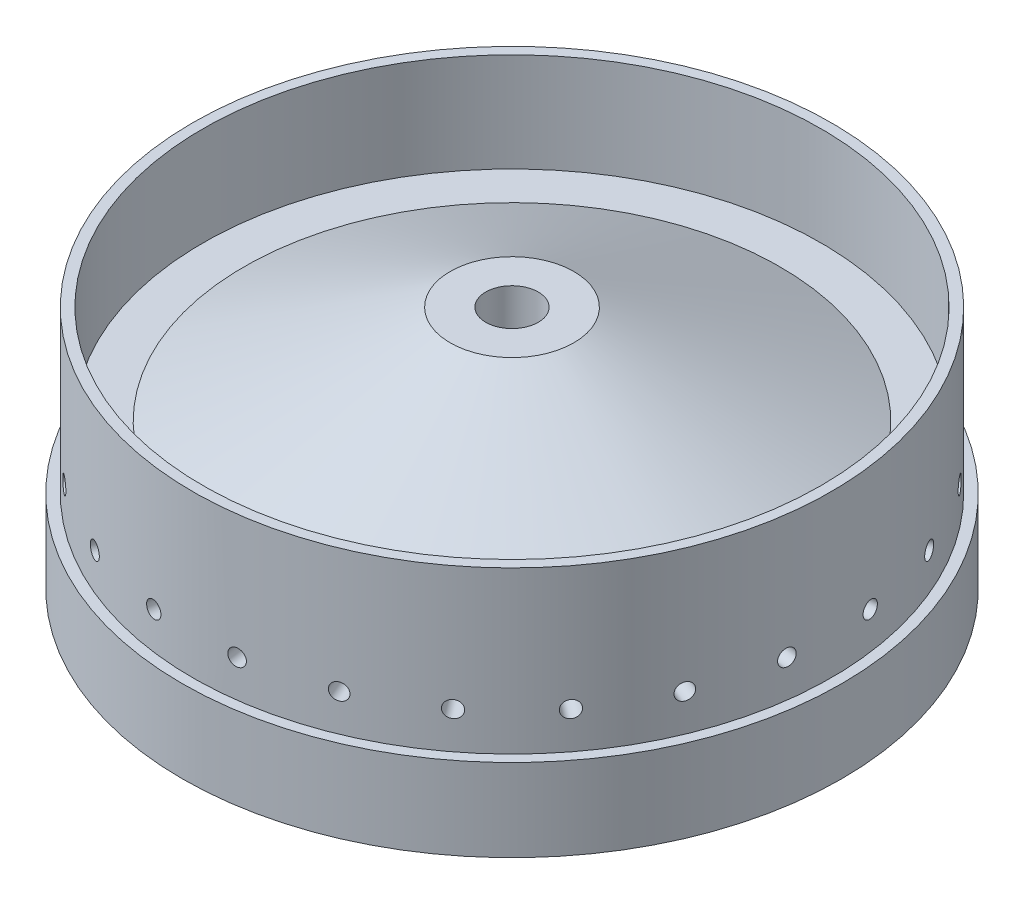
SolidWorks part; units mm, degrees
material "6061-T4 (SS)"
ref_plane "Front Plane" through (0, 0, 0) normal (0, 0, 1) x (1, 0, 0)
ref_plane "Top Plane" through (0, 0, 0) normal (0, 1, 0) x (1, 0, 0)
ref_plane "Right Plane" through (0, 0, 0) normal (1, 0, 0) x (0, 0, -1)
ref_plane "Plane1" through (0, 0, -75.0887) normal (0, 0, 1) x (1, 0, 0)
sketch "Sketch1" plane through (0, 0, 0) normal (0, 1, 0) x (1, 0, 0)
  line L1 (95.25, 0) -> (101.6, 0)
  line L2 (0, 0) -> (0, 61.9125) construction
  line L4 (101.6, 59.4931) -> (101.6, 0)
  line L6 (101.6, 59.4931) -> (8.0962, 59.4931) construction
  line L8 (0, 75.0887) -> (101.6, 75.0887)
  line L9 (101.6, 75.0887) -> (101.6, 59.4931)
  line L10 (8.0962, 0) -> (8.0962, 75.0887)
  line L11 (8.0962, 75.0887) -> (-8.0962, 75.0887)
  line L12 (-8.0962, 75.0887) -> (-8.0962, 0)
  line L13 (-8.0962, 0) -> (8.0962, 0)
  line L14 (8.0962, 59.4931) -> (0, 59.4931) construction
  line L15 (19.05, 75.0887) -> (82.55, 44.6088)
  line L16 (82.55, 44.6088) -> (95.25, 44.6088)
  line L17 (95.25, 44.6088) -> (95.25, 75.0887)
  ellipse E0 centre (0, 0) end of major axis (-95.25, 0) minor radius 59.4931
  point P18 (19.05, 75.0887)
  dimension "D4" = 15.5956
  dimension "D6" = 16.1925
  dimension "D7" = 6.35
  dimension "D8" = 30.48
  dimension "D9" = 12.7
  dimension "D10" = 19.05
  dimension "D2" = 101.6
  dimension "D3" = 75.0887
revolve "Revolve1" add sketch "Sketch1" angle 360 about L2
sketch "Sketch3" plane through (0, 0, 0) normal (0, 0, -1) x (-1, 0, 0)
  circle A0 centre (0, 0) radius 101.6
  circle A1 centre (0, 0) radius 98.425
  dimension "D1" = 203.2
  dimension "D2" = 3.175
extrude "Cut-Extrude2" cut sketch "Sketch3" along normal through all from offset 25.4
hole_wizard "1/4-20 Tapped Hole1" positions "3DSketch1" profile "Sketch10" tap size "1/4-20" standard "ANSI Inch"
sketch3d "3DSketch1"
  line L0 (97.583, 12.847, -36.83) -> (97.583, 12.847, 0) construction
  line L1 (97.583, 12.847, 0) -> (0, 0, 0) construction
  line L2 (0, 0, 0) -> (101.6, 0, 0) construction
  circle A0 centre (0, 0, 0) radius 101.6 construction
  point P0 (97.583, 12.847, -36.83)
  point P12 (0, 0, 101.6)
  dimension "D1" = 36.83
  dimension "D2" = 7.5
sketch "Sketch10" plane through (97.583, 12.847, -36.83) normal (0, 0, 1) x (-0.1305, 0.9914, 0)
  line L0 (0, 0) -> (0, 14.2338)
  line L1 (0, 14.2338) -> (2.5527, 12.7)
  line L2 (2.5527, 12.7) -> (2.5527, 0)
  line L5 (2.5527, 0) -> (0, 0)
  line L10 (0, 14.2338) -> (-2.5527, 12.7) construction
  line L11 (0, -6.35) -> (0, 107.95) construction
  dimension "Tap Drill Dia." = 5.1054
  dimension "Tap Drill Depth" = 12.7
  dimension "Drill Angle" = 118
cosmetic thread "Hole Thread2" parameters "D1"=12.7, "D2"=6.35
pattern_circular "CirPattern1" count 24 over 360 of "1/4-20 Tapped Hole1"
sketch "Sketch13" plane through (0, 0, 0) normal (0, 0, 1) x (1, 0, 0)
  line L0 (-67.9108, -66.7883) -> (66.7883, 67.9108)
  line L1 (-66.7883, -67.9108) -> (67.9108, 66.7883)
  line L2 (0, 0) -> (0, -28.3739) construction
  circle A4 centre (0, 0) radius 95.25 construction
  arc A5 (-67.9108, -66.7883) -> (-66.7883, -67.9108) centre (0, 0) ccw
  arc A6 (66.7883, 67.9108) -> (67.9108, 66.7883) centre (0, 0) cw
  dimension "D1" = 1.5875
  dimension "D2" = 135
sketch "Sketch14" plane through (0, 0, -75.0888) normal (0, 0, -1) x (-1, 0, 0)
  circle A0 centre (0, 0) radius 8.0962
  circle A1 centre (0, 0) radius 8.0962 construction
move or copy body "Body-Move/Copy1" bodies to move or copy 120 copy no rotation origin (0, 0, -37.5444) rotation axis (1, 0, 0) rotation angle 90
equation "\"D7@Sketch1\"= .25"
equation "\"D1@Plane1\"= \"D3@Sketch1\""
